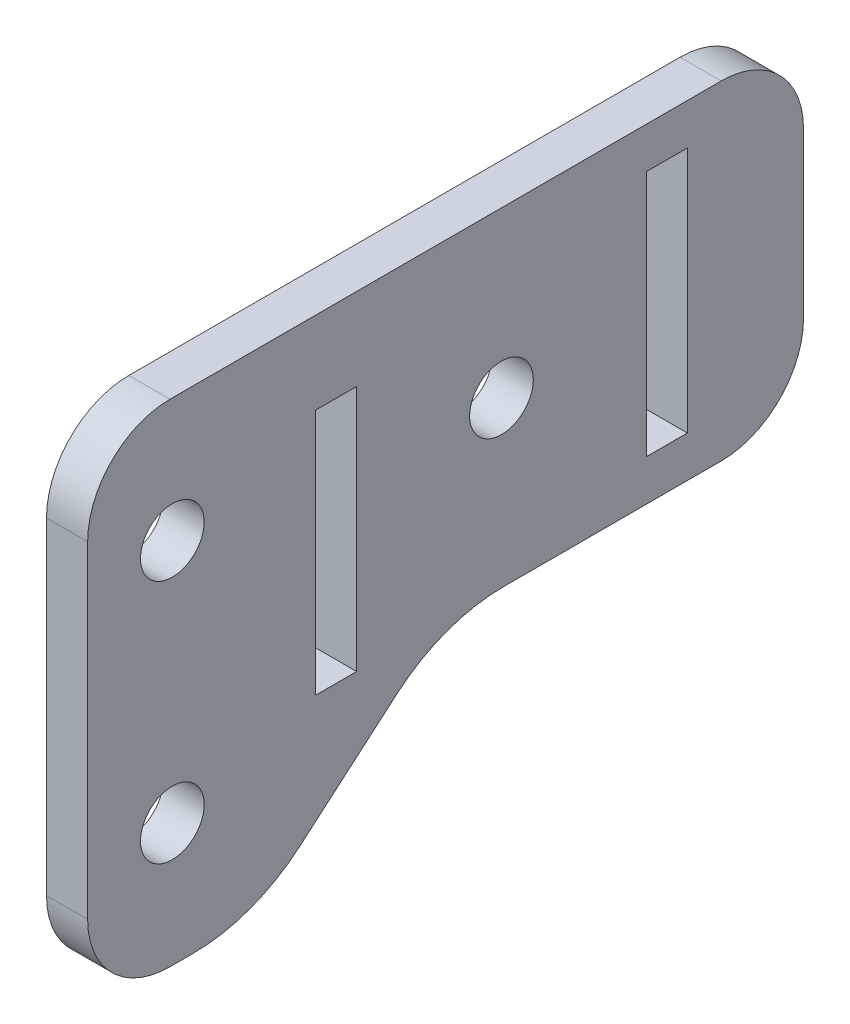
SolidWorks part; units mm, degrees
material "AISI 4340 Steel, annealed"
ref_plane "X-Y Datum" through (0, 0, 0) normal (0, 0, 1) x (1, 0, 0)
ref_plane "X-Z Datum" through (0, 0, 0) normal (0, 1, 0) x (1, 0, 0)
ref_plane "Y-Z Datum" through (0, 0, 0) normal (1, 0, 0) x (0, 0, -1)
sketch "Sketch1" plane through (0, 0, 0) normal (1, 0, 0) x (0, 0, -1)
  line L0 (23.3101, -8.1843) -> (23.3101, 17.2157) construction
  line L1 (-31.9349, 17.2157) -> (23.3101, 17.2157)
  line L2 (-31.9349, 17.2157) -> (-31.9349, -20.7167)
  line L5 (23.3101, -8.1843) -> (0.1935, -8.1843) construction
  line L6 (-8.0768, -11.2463) -> (-15.5452, -17.6547) construction
  line L7 (-23.8155, -20.7167) -> (-43.8887, -20.7167) construction
  line L8 (23.3101, -8.1843) -> (23.3101, 17.2157)
  line L9 (23.3101, -8.1843) -> (0.1935, -8.1843)
  line L10 (-8.0768, -11.2463) -> (-15.5452, -17.6547)
  line L11 (-23.8155, -20.7167) -> (-31.9349, -20.7167)
  arc A6 (0.1935, -8.1843) -> (-8.0768, -11.2463) centre (0.1935, -20.8843) ccw construction
  arc A7 (-23.8155, -20.7167) -> (-15.5452, -17.6547) centre (-23.8155, -8.0167) ccw construction
  arc A8 (0.1935, -8.1843) -> (-8.0768, -11.2463) centre (0.1935, -20.8843) ccw
  arc A9 (-23.8155, -20.7167) -> (-15.5452, -17.6547) centre (-23.8155, -8.0167) ccw
  point P0 (0, 0)
  point P1 (0, 0)
  point P5 (0, 0)
  point P7 (0, 0)
  point P9 (0, 0)
  point P13 (0, 0)
  dimension "D2" = 55.245
extrude "Boss-Extrude1" add sketch "Sketch1" along normal blind 3.175
sketch "Sketch7" plane through (0, 0, 0) normal (-1, 0, 0) x (0, 0, 1)
  line L0 (-11.176, 14.0407) -> (-14.351, 14.0407)
  line L1 (-11.176, 14.0407) -> (-11.176, -5.0093)
  line L2 (-11.176, -5.0093) -> (-14.351, -5.0093)
  line L3 (-14.351, -5.0093) -> (-14.351, 14.0407)
  line L4 (14.351, 10.8657) -> (11.176, 10.8657)
  line L5 (11.176, 10.8657) -> (11.176, -8.1843)
  line L6 (11.176, -8.1843) -> (14.351, -8.1843)
  line L7 (14.351, -8.1843) -> (14.351, 10.8657)
  line L8 (-23.3101, 17.2157) -> (31.9349, 17.2157) construction
  line L11 (-0.1935, -8.1843) -> (-23.3101, -8.1843) construction
  point P6 (0, 0)
  point P8 (0, 0)
  point P10 (-11.176, -4.923)
  point P12 (14.351, 1.3407)
  dimension "D1" = 3.175
  dimension "D2" = 19.05
  dimension "D3" = 15.875
  dimension "D4" = 22.352
  dimension "D5" = 19.05
  dimension "D6" = 3.175
  dimension "D7" = 3.175
  dimension "D8" = 11.176
extrude "Cut-Extrude1" cut sketch "Sketch7" against normal blind 3.175
sketch "Sketch4" plane through (0, 0, 0) normal (-1, 0, 0) x (0, 0, 1)
  point P0 (19.05, 4.7625)
  point P1 (-15.875, -5.3975)
  point P2 (19.05, -15.5575)
  dimension "D1" = 20.32
  dimension "D2" = 15.5575
  dimension "D3" = 19.05
  dimension "D4" = 15.875
  dimension "D5" = 10.16
hole_wizard "#10 (0.1935) Diameter Hole1" positions "Sketch5" profile "Sketch6" hole size "#10" standard "ANSI Inch"
sketch "Sketch5" plane through (0, 0, 0) normal (-1, 0, 0) x (0, 0, 1)
  line L0 (-23.3101, 17.2157) -> (31.9349, 17.2157) construction
  line L1 (31.9349, -20.7167) -> (23.8155, -20.7167) construction
  line L2 (14.351, -8.1843) -> (14.351, 10.8657) construction
  point P0 (25.4, 7.6907)
  point P3 (25.4, -11.1917)
  point P6 (0, 4.5157)
  point P12 (0, 0)
  point P13 (0, 0)
  point P18 (0, 0)
  dimension "D1" = 12.7
  dimension "D2" = 9.525
  dimension "D3" = 9.525
  dimension "D4" = 11.049
sketch "Sketch6" plane through (0, 7.6907, 25.4) normal (0, 1, 0) x (0, 0, 1)
  line L0 (0, 0) -> (0, 11.176)
  line L1 (0, 11.176) -> (2.4574, 9.6994)
  line L2 (2.4574, 9.6994) -> (2.4574, 0)
  line L5 (2.4574, 0) -> (0, 0)
  line L10 (0, 11.176) -> (-2.4575, 9.6994) construction
  line L11 (0, -6.35) -> (0, 107.95) construction
  dimension "Hole Dia." = 4.9149
  dimension "Hole Depth" = 11.176
  dimension "Drill Angle" = 118
fillet "Fillet1" radius 6.35 4 edges at (1.5875, 17.2157, 31.9349) (1.5875, 17.2157, -23.3101) (1.5875, -8.1843, -23.3101) (1.5875, -20.7167, 31.9349)
